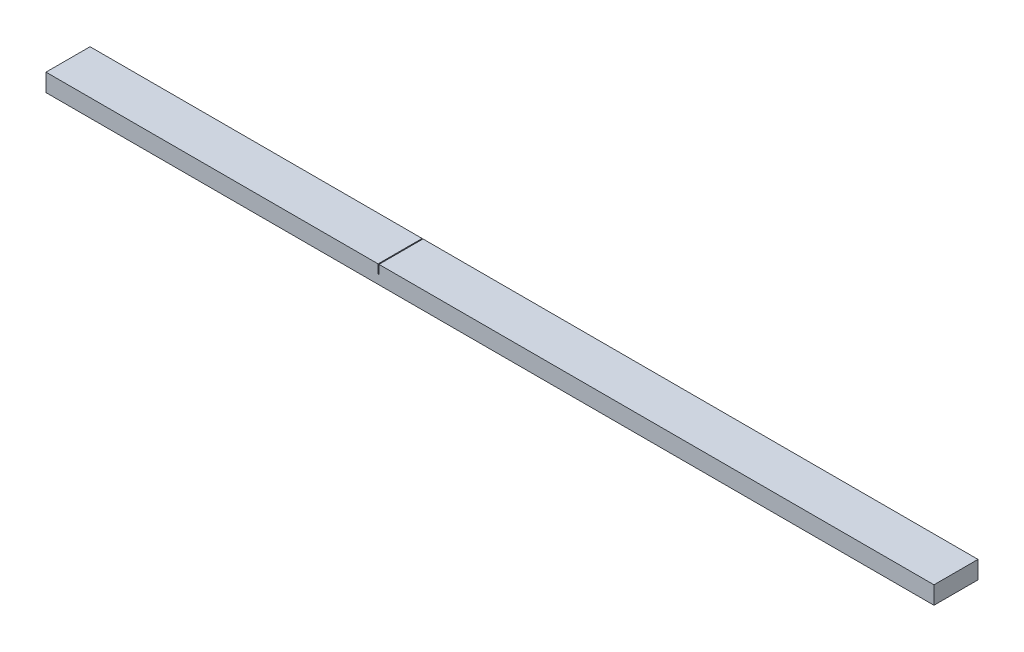
SolidWorks part; units mm, degrees
ref_plane "Front Plane" through (0, 0, 0) normal (0, 0, 1) x (1, 0, 0)
ref_plane "Top Plane" through (0, 0, 0) normal (0, 1, 0) x (1, 0, 0)
ref_plane "Right Plane" through (0, 0, 0) normal (1, 0, 0) x (0, 0, -1)
sketch "Sketch1" plane through (0, 0, 0) normal (1, 0, 0) x (0, 0, -1)
  line L1 (22.4912, 21.8138) -> (-27.0978, 21.8138)
  line L2 (22.4912, 21.8138) -> (22.4912, 1.8138)
  line L3 (22.4912, 1.8138) -> (-27.0978, 1.8138)
  line L4 (-27.0978, 21.8138) -> (-27.0978, 1.8138)
  dimension "D1" = 49.5891
  dimension "D2" = 20
extrude "Boss-Extrude1" add sketch "Sketch1" along normal blind 1000
sketch "Sketch2" plane through (0, 21.8138, 0) normal (0, 1, 0) x (1, 0, 0)
  line L0 (375, 22.4912) -> (375, -27.0978) construction
  line L1 (1000, 22.4912) -> (0, 22.4912) construction
  line L2 (1000, -27.0978) -> (0, -27.0978) construction
  line L3 (0, 22.4912) -> (0, -27.0978) construction
  line L5 (375, 22.4912) -> (374, 22.4912)
  line L6 (375, 22.4912) -> (375, -27.0978)
  line L7 (375, -27.0978) -> (374, -27.0978)
  line L8 (374, 22.4912) -> (374, -27.0978)
  dimension "D1" = 375
  dimension "D2" = 1
extrude "Cut-Extrude1" cut sketch "Sketch2" against normal blind 10
equation "\"0.0w\"=0.0384789"
